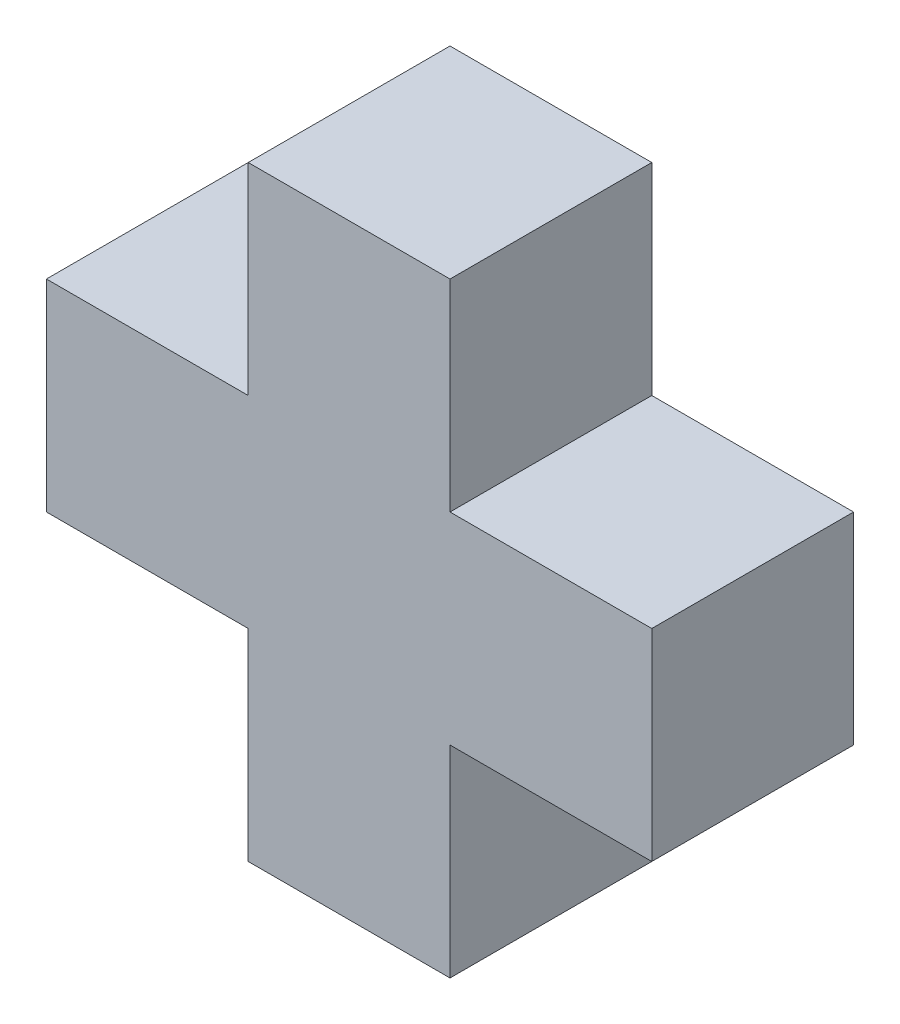
SolidWorks part; units mm, degrees
ref_plane "Front Plane" through (0, 0, 0) normal (0, 0, 1) x (1, 0, 0)
ref_plane "Top Plane" through (0, 0, 0) normal (0, 1, 0) x (1, 0, 0)
ref_plane "Right Plane" through (0, 0, 0) normal (1, 0, 0) x (0, 0, -1)
sketch "Sketch1" plane through (0, 0, 0) normal (0, 0, 1) x (1, 0, 0)
  line L20 (25.4, 0) -> (25.4, 25.4)
  line L21 (25.4, 25.4) -> (0, 25.4)
  line L22 (0, 25.4) -> (0, 50.8)
  line L23 (0, 50.8) -> (25.4, 50.8)
  line L24 (25.4, 50.8) -> (25.4, 76.2)
  line L25 (25.4, 76.2) -> (50.8, 76.2)
  line L26 (50.8, 76.2) -> (50.8, 50.8)
  line L27 (50.8, 50.8) -> (76.2, 50.8)
  line L28 (76.2, 50.8) -> (76.2, 25.4)
  line L29 (76.2, 25.4) -> (50.8, 25.4)
  line L30 (50.8, 25.4) -> (50.8, 0)
  line L31 (50.8, 0) -> (25.4, 0)
extrude "Boss-Extrude1" add sketch "Sketch1" along normal blind 25.4
